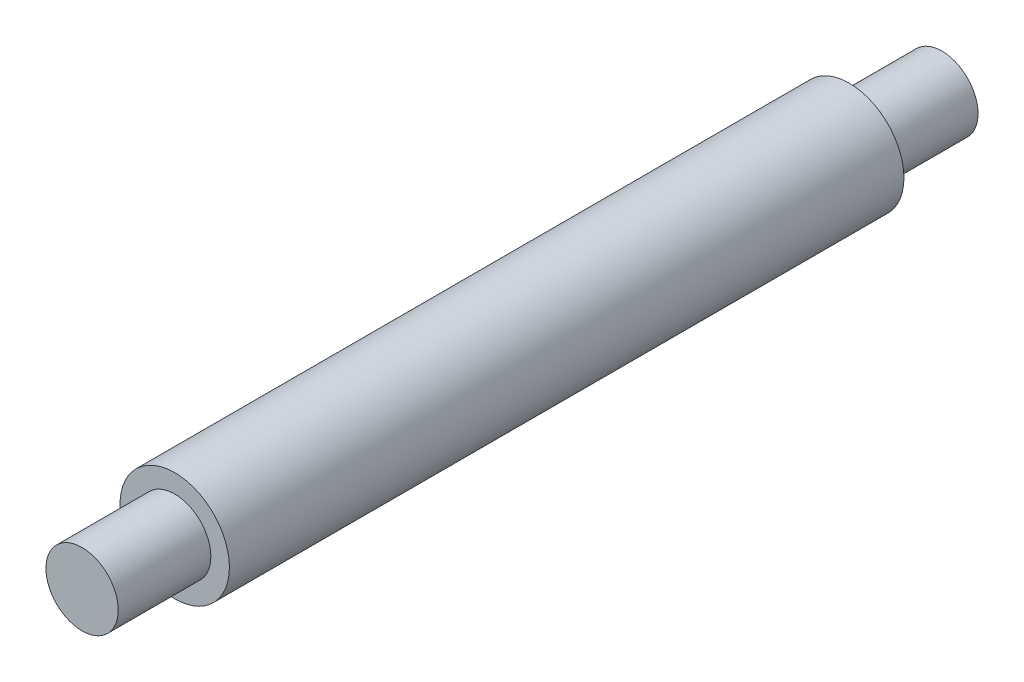
SolidWorks part; units mm, degrees
ref_plane "正面" through (0, 0, 0) normal (0, 0, 1) x (1, 0, 0)
ref_plane "平面" through (0, 0, 0) normal (0, 1, 0) x (1, 0, 0)
ref_plane "右側面" through (0, 0, 0) normal (1, 0, 0) x (0, 0, -1)
sketch "ｽｹｯﾁ1" plane through (0, 0, 0) normal (0, 0, 1) x (1, 0, 0)
  circle A0 centre (0, 0) radius 2.95
  dimension "D1" = 5.9
extrude "ﾎﾞｽ - 押し出し1" add sketch "ｽｹｯﾁ1" along normal blind 36.4
sketch "ｽｹｯﾁ2" plane through (0, 0, 36.4) normal (0, 0, 1) x (1, 0, 0)
  circle A0 centre (0, 0) radius 1.95
  dimension "D1" = 3.9
extrude "ﾎﾞｽ - 押し出し2" add sketch "ｽｹｯﾁ2" along normal blind 5
sketch "ｽｹｯﾁ3" plane through (0, 0, 0) normal (0, 0, -1) x (-1, 0, 0)
  circle A0 centre (0, 0) radius 1.95
  dimension "D1" = 3.9
extrude "ﾎﾞｽ - 押し出し3" add sketch "ｽｹｯﾁ3" along normal blind 5
